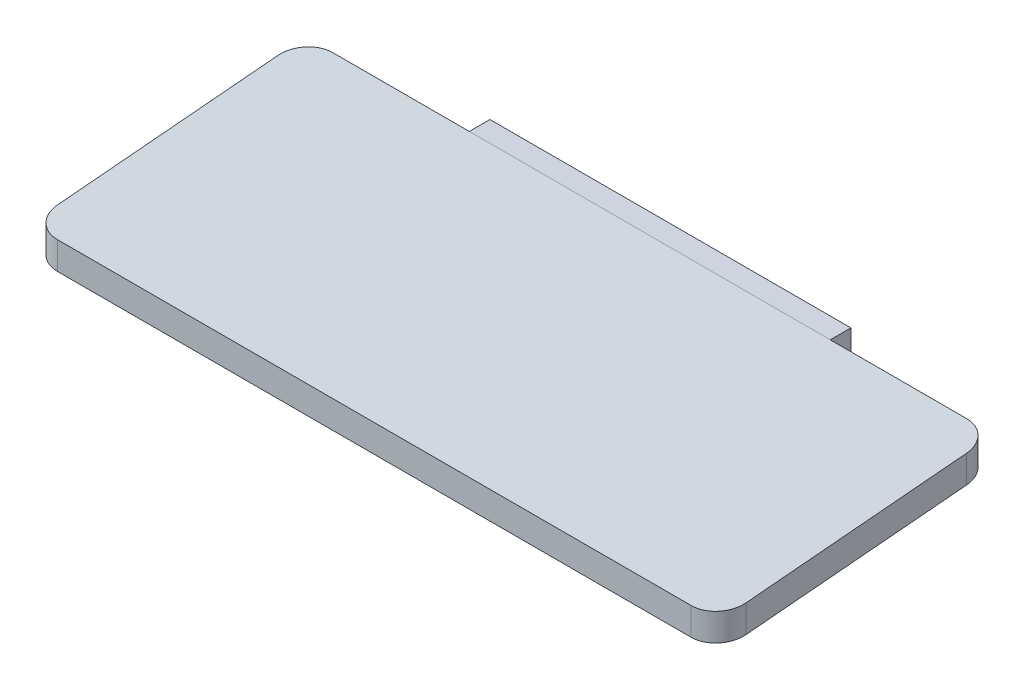
SolidWorks part; units mm, degrees
ref_plane "Front Plane" through (0, 0, 0) normal (0, 0, 1) x (1, 0, 0)
ref_plane "Top Plane" through (0, 0, 0) normal (0, 1, 0) x (1, 0, 0)
ref_plane "Right Plane" through (0, 0, 0) normal (1, 0, 0) x (0, 0, -1)
ref_plane "Plane1" through (-57.9, 36, -26.2) normal (0, -1, 0) x (-1, 0, 0)
sketch "Sketch3" plane through (0, 0, 0) normal (0, 0, 1) x (1, 0, 0)
  line L1 (-8, 46) -> (8, 46) construction
  line L2 (-13.1, 39.9) -> (13.1, 39.9)
  line L3 (-13.1, 39.9) -> (-13.1, 55.9)
  line L4 (-13.1, 55.9) -> (13.1, 55.9)
  line L5 (13.1, 39.9) -> (13.1, 55.9)
  circle A0 centre (8, 46) radius 2.1 construction
  circle A1 centre (-8, 46) radius 2.1 construction
  circle A2 centre (8, 46) radius 2.1
  circle A3 centre (-8, 46) radius 2.1
  point P6 (0, 46)
  point P7 (0, 39.9)
  point P12 (0, 0)
  point P13 (0, 55.9)
  dimension "D1" = 4
  dimension "D2" = 3
  dimension "D3" = 16
extrude "Boss-Extrude1" add sketch "Sketch3" along normal blind 1.5
sketch "Sketch4" plane through (13.1, 0, 0) normal (1, 0, 0) x (0, 0, -1)
  line L0 (-54, -61.5) -> (-354, -61.5) construction
  line L1 (-354, -61.5) -> (-354, -51.5) construction
  line L2 (-354, -51.5) -> (-54, -51.5) construction
  line L3 (-54, -51.5) -> (-54, -31.5) construction
  line L4 (-54, 98.5) -> (-54, -51.5) construction
  line L5 (-54, -31.5) -> (-354, -31.5) construction
  line L6 (-354, -31.5) -> (-354, -51.5) construction
  line L7 (-204, -31.5) -> (-204, -11.5) construction
  line L8 (-204, -11.5) -> (-354, -11.5) construction
  line L9 (-354, -11.5) -> (-354, -31.5) construction
  line L10 (-204, -11.5) -> (-4, 66.05) construction
  line L11 (-4, 73) -> (-4, 59.1) construction
  line L12 (-1.5, 55.9) -> (-21.5, 54.1502)
  line L13 (-21.5, 54.1502) -> (-21.5, 52.1502)
  line L14 (-21.5, 52.1502) -> (-1.5, 53.9)
  line L15 (-1.5, 39.9) -> (-1.5, 55.9) construction
  line L16 (-1.5, 53.9) -> (-1.5, 55.9)
  line L17 (-1.5, 55.9) -> (0, 55.9) construction
  dimension "D1" = 300
  dimension "D2" = 20
  dimension "D3" = 20
  dimension "D4" = 20
  dimension "D5" = 2
  dimension "D6" = 5
extrude "Boss-Extrude2" add sketch "Sketch4" against normal mid plane 50 from vertex at -13.1 starting at point (0, 55.9, 0)
chamfer "Chamfer1" distance 3 angle 45 1 edges at (0, 53.9, 1.5)
fillet "Fillet1" radius 2 6 edges at (-13.1, 39.9, 0.75) (13.1, 39.9, 0.75) (25, 54.9, 1.5) (-25, 54.9, 1.5) (-25, 53.1502, 21.5) (25, 53.1502, 21.5)
